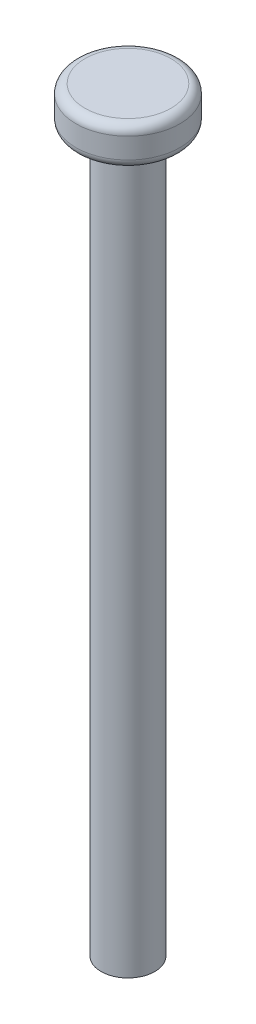
SolidWorks part; units mm, degrees
ref_plane "Спереди" through (0, 0, 0) normal (0, 0, 1) x (1, 0, 0)
ref_plane "Сверху" through (0, 0, 0) normal (0, 1, 0) x (1, 0, 0)
ref_plane "Справа" through (0, 0, 0) normal (1, 0, 0) x (0, 0, -1)
sketch "Sketch1" plane through (0, 0, 0) normal (0, 1, 0) x (1, 0, 0)
  circle A0 centre (0, 0) radius 3
  dimension "D1" = 6
extrude "Boss-Extrude1" add sketch "Sketch1" along normal blind 80
sketch "Sketch2" plane through (0, 80, 0) normal (0, 1, 0) x (1, 0, 0)
  circle A0 centre (0, 0) radius 5.8
  dimension "D1" = 11.6
extrude "Boss-Extrude2" add sketch "Sketch2" along normal blind 4.3
fillet "Fillet1" radius 1 2 edges at (0, 80, 5.8) (0, 84.3, 5.8)
